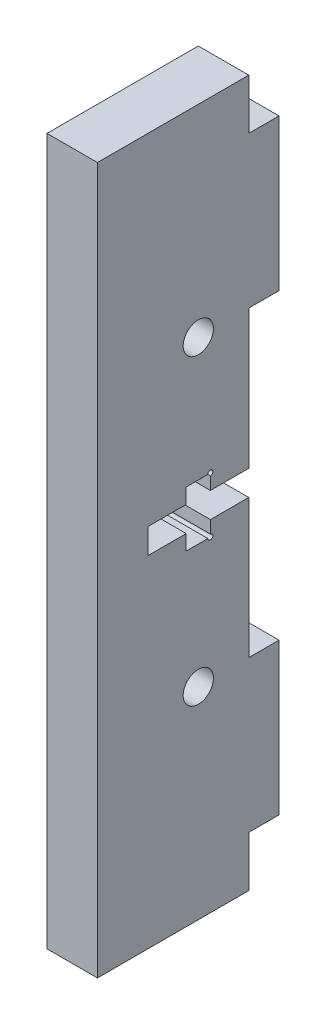
SolidWorks part; units mm, degrees
material "PMMA"
ref_plane "Front Plane" through (0, 0, 0) normal (0, 0, 1) x (1, 0, 0)
ref_plane "Top Plane" through (0, 0, 0) normal (0, 1, 0) x (1, 0, 0)
ref_plane "Right Plane" through (0, 0, 0) normal (1, 0, 0) x (0, 0, -1)
sketch "Schizzo1" plane through (0, 0, 0) normal (1, 0, 0) x (0, 0, -1)
  line L0 (-7.5, 35) -> (7.5, -35) construction
  line L1 (-7.5, 35) -> (7.5, 35)
  line L2 (-7.5, 35) -> (-7.5, -35)
  line L3 (-7.5, -35) -> (7.5, -35)
  line L4 (7.5, 35) -> (7.5, -35)
  point P4 (0, 0)
  dimension "D1" = 70
  dimension "D2" = 15
extrude "Estrusione-Estrusione1" add sketch "Schizzo1" along normal blind 5
sketch "Schizzo2" plane through (0, 0, -7.5) normal (0, 0, -1) x (-1, 0, 0)
  line L0 (-5, 0) -> (0, 0) construction
  line L1 (-5, 30) -> (0, 30)
  line L2 (-5, 30) -> (-5, 15)
  line L3 (-5, 15) -> (0, 15)
  line L4 (0, 30) -> (0, 15)
  line L5 (-5, -35) -> (-5, 35) construction
  line L7 (0, -35) -> (0, 35) construction
  line L8 (-5, -30) -> (-5, -15)
  line L9 (-5, -15) -> (0, -15)
  line L10 (0, -30) -> (0, -15)
  line L11 (-5, -30) -> (0, -30)
  dimension "D1" = 15
  dimension "D2" = 15
extrude "Estrusione-Estrusione2" add sketch "Schizzo2" along normal blind 3
sketch "Schizzo4" plane through (0, 0, 0) normal (1, 0, 0) x (0, 0, -1)
  line L0 (2.5, 35) -> (2.5, -35) construction
  line L1 (7.5, 35) -> (-7.5, 35) construction
  line L2 (-7.5, -35) -> (7.5, -35) construction
  line L3 (7.5, 30) -> (7.5, 35) construction
  line L4 (7.5, 0) -> (-7.5, 0) construction
  line L5 (7.5, -15) -> (7.5, 15) construction
  line L6 (-7.5, 35) -> (-7.5, -35) construction
  line L7 (7.5, 30) -> (7.5, 35) construction
  line L8 (10.5, 15) -> (-7.5, 15) construction
  line L9 (8.9133, 0) -> (18.9133, 0) construction
  line L10 (-2.5, 1.25) -> (1.3, 1.25)
  line L11 (1.3, 1.25) -> (1.3, 2.75)
  line L12 (1.3, 2.75) -> (3.7, 2.75)
  line L13 (3.7, 2.75) -> (3.7, 1.25)
  line L14 (3.7, 1.25) -> (7.5, 1.25)
  line L15 (7.5, 1.25) -> (7.5, -1.25)
  line L16 (7.5, -1.25) -> (3.7, -1.25)
  line L17 (3.7, -1.25) -> (3.7, -2.75)
  line L18 (3.7, -2.75) -> (1.3, -2.75)
  line L19 (1.3, -2.75) -> (1.3, -1.25)
  line L20 (1.3, -1.25) -> (-2.5, -1.25)
  line L21 (-2.5, -1.25) -> (-2.5, 1.25)
  line L22 (24.8004, 0) -> (9.8004, 0) construction
  circle A1 centre (2.5, 15) radius 1.5
  circle A2 centre (2.5, -15) radius 1.5
  dimension "D2" = 3
  dimension "D3" = 20
  dimension "D1" = 5
  dimension "D4" = 5.5
  dimension "D5" = 2.5
  dimension "D6" = 1.25
  dimension "D7" = 2.75
  dimension "D8" = 2.4
  dimension "D9" = 10
extrude "Taglio-Estrusione2" cut sketch "Schizzo4" along direction (1, 0, 0) on the side of the normal through all
sketch "Schizzo5" plane through (5, 0, 0) normal (1, 0, 0) x (0, 0, -1)
  circle A0 centre (3.7, 2.75) radius 0.25
  circle A1 centre (3.7, -2.75) radius 0.25
  dimension "D1" = 0.5
extrude "Taglio-Estrusione3" cut sketch "Schizzo5" against normal blind 10
equation "\"Thickness5\"=5"
equation "\"D1@Estrusione-Estrusione1\"=\"Thickness5\""
equation "\"Thickness3\"=3"
equation "\"D1@Estrusione-Estrusione2\"=\"Thickness3\""
